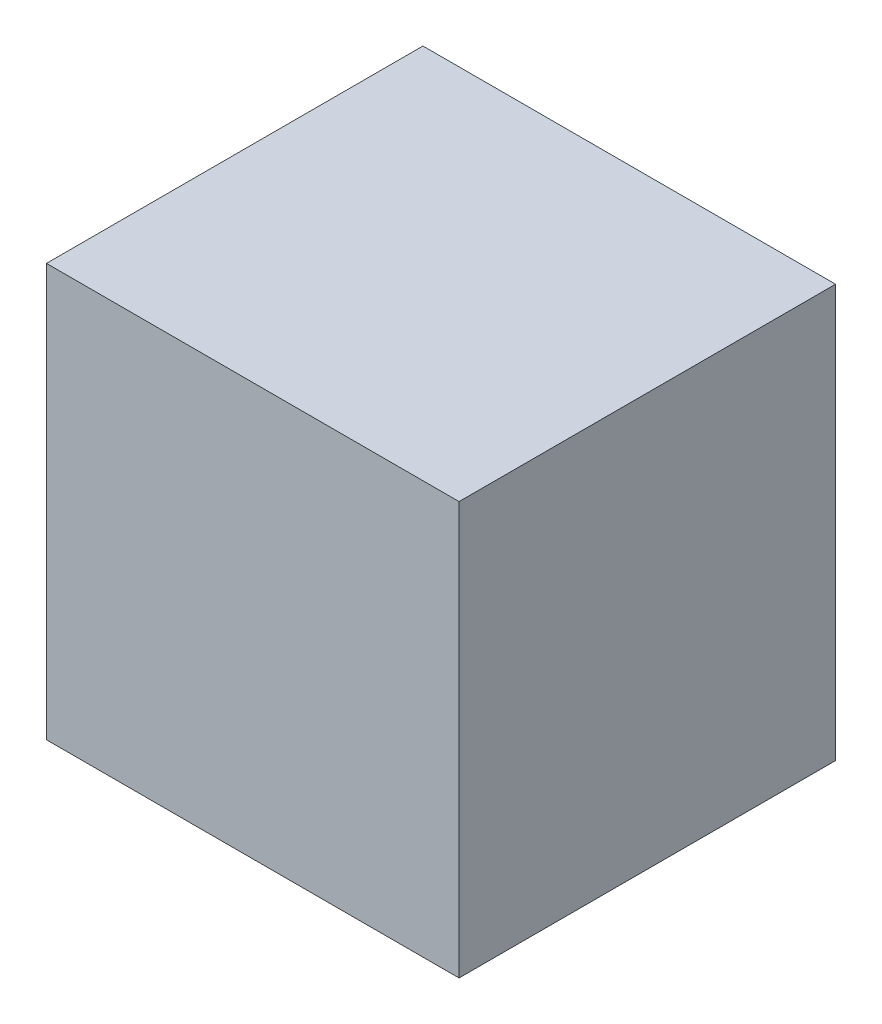
SolidWorks part; units mm, degrees
ref_plane "Front" through (0, 0, 0) normal (0, 0, 1) x (1, 0, 0)
ref_plane "Top" through (0, 0, 0) normal (0, 1, 0) x (1, 0, 0)
ref_plane "Right" through (0, 0, 0) normal (1, 0, 0) x (0, 0, -1)
sketch "Sketch1" plane through (0, 0, 0) normal (0, 1, 0) x (1, 0, 0)
  line L1 (0, 0) -> (254, 0)
  line L2 (0, 0) -> (0, 231.775)
  line L3 (0, 231.775) -> (254, 231.775)
  line L4 (254, 0) -> (254, 231.775)
  dimension "D1" = 231.775
  dimension "D2" = 254
extrude "Boss-Extrude1" add sketch "Sketch1" along normal blind 254
